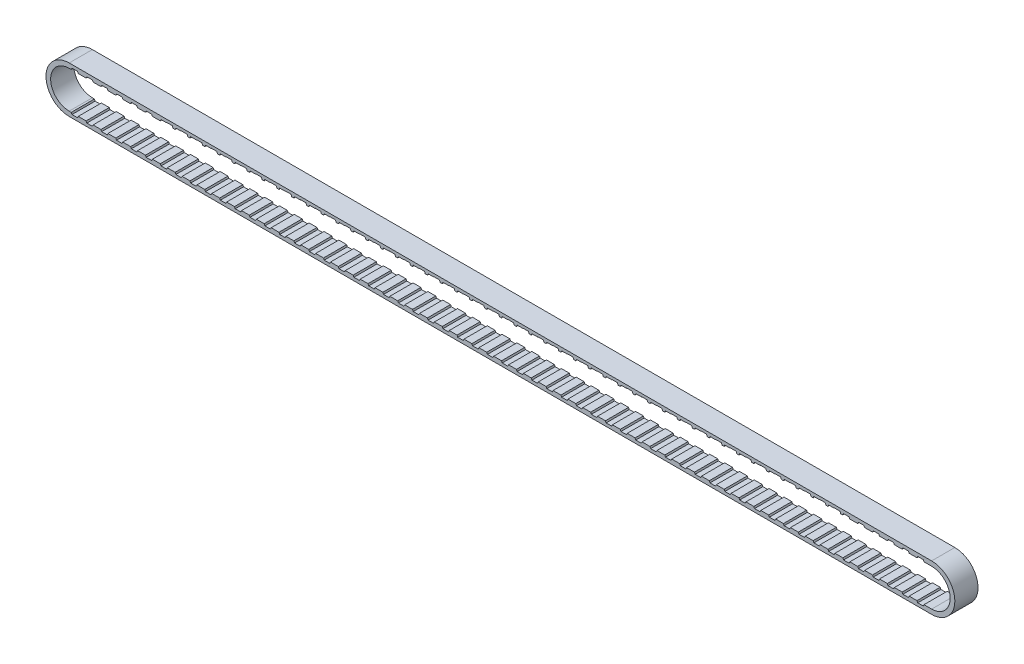
SolidWorks part; units mm, degrees
ref_plane "Front Plane" through (0, 0, 0) normal (0, 0, 1) x (1, 0, 0)
ref_plane "Top Plane" through (0, 0, 0) normal (0, 1, 0) x (1, 0, 0)
ref_plane "Right Plane" through (0, 0, 0) normal (1, 0, 0) x (0, 0, -1)
sketch "Sketch1" plane through (0, 0, 0) normal (0, 0, 1) x (1, 0, 0)
  line L1 (-118.11, 6.35) -> (118.11, 6.35)
  line L2 (-118.11, 5.08) -> (118.11, 5.08)
  line L3 (-118.11, -6.35) -> (118.11, -6.35)
  line L5 (-118.11, 6.35) -> (118.11, -6.35) construction
  line L6 (-118.11, -6.35) -> (118.11, 6.35) construction
  line L7 (-118.11, -5.08) -> (118.11, -5.08)
  line L9 (-118.11, 5.08) -> (118.11, -5.08) construction
  line L10 (-118.11, -5.08) -> (118.11, 5.08) construction
  arc A0 (-118.11, 6.35) -> (-118.11, -6.35) centre (-118.11, 0) ccw
  arc A1 (118.11, 6.35) -> (118.11, -6.35) centre (118.11, 0) cw
  arc A2 (-118.11, 5.08) -> (-118.11, -5.08) centre (-118.11, 0) ccw
  arc A3 (118.11, 5.08) -> (118.11, -5.08) centre (118.11, 0) cw
  point P0 (0, 0)
  point P8 (0, 0)
  point P15 (-124.46, 0)
  point P16 (124.46, 0)
  dimension "D2" = 6.35
  dimension "D4" = 236.22
  dimension "D1" = 236.22
  dimension "D3" = 1.27
  dimension "D5" = 236.22
extrude "Boss-Extrude1" add sketch "Sketch1" against normal blind 6.35
sketch "Sketch2" plane through (0, 0, 0) normal (0, 0, 1) x (1, 0, 0)
  line L0 (-85.09, -4.953) -> (-83.058, -4.953)
  line L3 (-83.058, -4.953) -> (-83.312, -5.5007)
  line L4 (-83.312, -5.5007) -> (-84.836, -5.5007)
  line L6 (-84.836, -5.5007) -> (-85.09, -4.953)
  line L7 (-118.11, -5.08) -> (118.11, -5.08) construction
  dimension "D1" = 0.127
  dimension "D2" = 1.524
  dimension "D3" = 2.032
extrude "Cut-Extrude1" cut sketch "Sketch2" against normal blind 8.89
pattern_linear "LPattern3" count 50 spacing 4.064 along (1, 0, 0) count 9 spacing 4.064 along (-1, 0, 0) of "Cut-Extrude1"
mirror "Mirror3" about plane through (0, 0, 0) normal (0, 1, 0) of "Cut-Extrude1", "LPattern3"
sketch "Sketch3" plane through (0, 0, 0) normal (0, 0, 1) x (1, 0, 0)
  line L0 (-91.6459, 4.953) -> (-89.6139, 4.953)
  line L1 (-89.6139, 4.953) -> (-89.8679, 5.588)
  line L2 (-89.8679, 5.588) -> (-91.3919, 5.588)
  line L3 (-91.3919, 5.588) -> (-91.6459, 4.953)
  line L4 (118.11, 6.35) -> (-118.11, 6.35) construction
  dimension "D1" = 2.032
  dimension "D2" = 0.635
  dimension "D3" = 0.762
  dimension "D4" = 1.524
extrude "Cut-Extrude2" cut sketch "Sketch3" against normal blind 8.89
pattern_linear "LPattern2" count 46 spacing 4.064 along (1, 0, 0) of "Cut-Extrude2"
